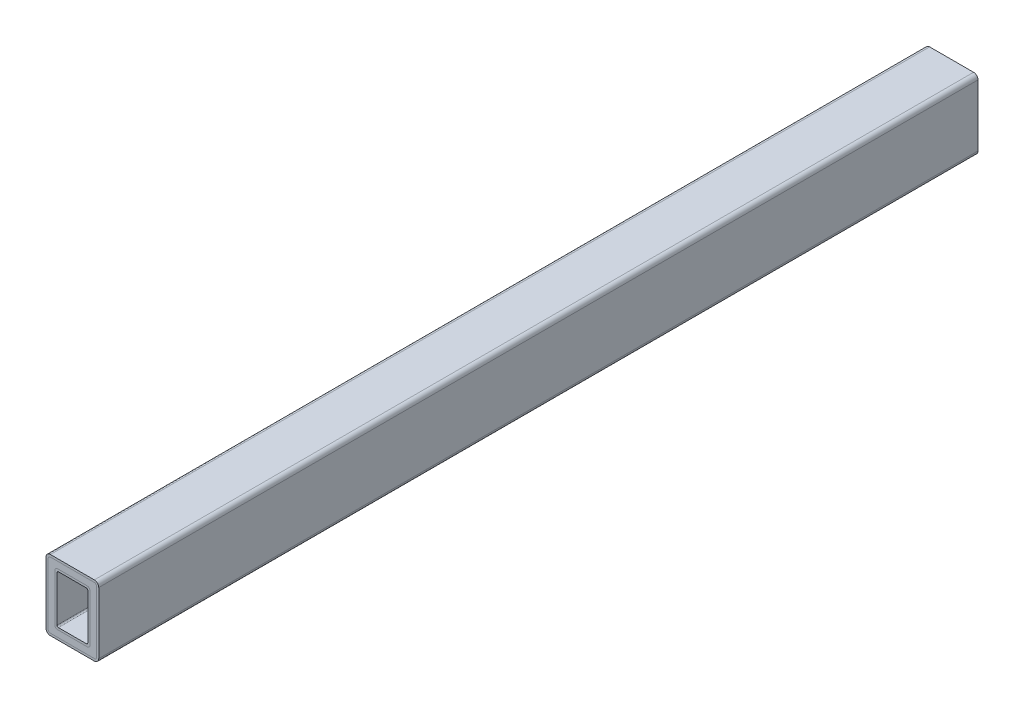
SolidWorks part; units mm, degrees
material "Plain Carbon Steel"
ref_plane "Front Plane" through (0, 0, 0) normal (0, 0, 1) x (1, 0, 0)
ref_plane "Top Plane" through (0, 0, 0) normal (0, 1, 0) x (1, 0, 0)
ref_plane "Right Plane" through (0, 0, 0) normal (1, 0, 0) x (0, 0, -1)
sketch "Sketch4" plane through (0, 0, 0) normal (0, 0, 1) x (1, 0, 0)
  line L4 (31.75, -47.6907) -> (-31.75, -47.6907)
  line L5 (34.925, 44.3843) -> (34.925, -44.5157)
  line L6 (-34.925, -44.5157) -> (-34.925, 44.3843)
  line L7 (-31.75, 47.5593) -> (31.75, 47.5593)
  line L8 (31.75, -50.8657) -> (-31.75, -50.8657)
  line L9 (38.1, 44.3843) -> (38.1, -44.5157)
  line L10 (-31.75, 50.7343) -> (31.75, 50.7343)
  line L11 (-38.1, -44.5157) -> (-38.1, 44.3843)
  arc A4 (-34.925, -44.5157) -> (-31.75, -47.6907) centre (-31.75, -44.5157) ccw
  arc A5 (31.75, -47.6907) -> (34.925, -44.5157) centre (31.75, -44.5157) ccw
  arc A6 (34.925, 44.3843) -> (31.75, 47.5593) centre (31.75, 44.3843) ccw
  arc A7 (-31.75, 47.5593) -> (-34.925, 44.3843) centre (-31.75, 44.3843) ccw
  arc A8 (-38.1, -44.5157) -> (-31.75, -50.8657) centre (-31.75, -44.5157) ccw
  arc A9 (31.75, -50.8657) -> (38.1, -44.5157) centre (31.75, -44.5157) ccw
  arc A10 (38.1, 44.3843) -> (31.75, 50.7343) centre (31.75, 44.3843) ccw
  arc A11 (-31.75, 50.7343) -> (-38.1, 44.3843) centre (-31.75, 44.3843) ccw
  dimension "D1" = 3.175
extrude "Boss-Extrude1" add sketch "Sketch4" along normal mid plane 1270 separate body
sketch "Sketch5" [suppressed] plane through (0, 50.7343, 0) normal (0, 1, 0) x (1, 0, 0)
  line L0 (0, 635) -> (0, 130) construction
  line L1 (31.75, 635) -> (-31.75, 635) construction
  line L2 (0, 130) -> (0, -130) construction
  line L3 (0, -130) -> (0, -635) construction
  line L4 (31.75, -635) -> (-31.75, -635) construction
  line L5 (-38.1, 130) -> (38.1, 130)
  line L6 (-38.1, -635) -> (-38.1, 635) construction
  line L7 (38.1, -635) -> (38.1, 635) construction
  line L8 (-38.1, -130) -> (38.1, -130)
  dimension "D1" = 260
split line "Split Line1" [suppressed]
sketch "Sketch6" [suppressed] plane through (0, 0, 0) normal (0, 0, 1) x (1, 0, 0)
  circle A0 centre (0, 0) radius 3.0965
extrude "Boss-Extrude2" [suppressed] add sketch "Sketch6" along normal mid plane 35.814 separate body
sketch "Sketch7" [suppressed] plane through (0, 0, 635) normal (0, 0, 1) x (1, 0, 0)
  line L0 (-31.75, -47.6907) -> (31.75, -47.6907) construction
  line L1 (34.925, -44.5157) -> (34.925, 44.3843) construction
  line L2 (-34.925, 44.3843) -> (-34.925, -44.5157) construction
  line L3 (31.75, 47.5593) -> (-31.75, 47.5593) construction
  line L4 (-31.75, -47.6907) -> (31.75, -47.6907)
  line L5 (34.925, -44.5157) -> (34.925, 44.3843)
  line L6 (-34.925, 44.3843) -> (-34.925, -44.5157)
  line L7 (31.75, 47.5593) -> (-31.75, 47.5593)
  arc A0 (-34.925, -44.5157) -> (-31.75, -47.6907) centre (-31.75, -44.5157) ccw construction
  arc A1 (31.75, -47.6907) -> (34.925, -44.5157) centre (31.75, -44.5157) ccw construction
  arc A2 (34.925, 44.3843) -> (31.75, 47.5593) centre (31.75, 44.3843) ccw construction
  arc A3 (-31.75, 47.5593) -> (-34.925, 44.3843) centre (-31.75, 44.3843) ccw construction
  arc A4 (-34.925, -44.5157) -> (-31.75, -47.6907) centre (-31.75, -44.5157) ccw
  arc A5 (31.75, -47.6907) -> (34.925, -44.5157) centre (31.75, -44.5157) ccw
  arc A6 (34.925, 44.3843) -> (31.75, 47.5593) centre (31.75, 44.3843) ccw
  arc A7 (-31.75, 47.5593) -> (-34.925, 44.3843) centre (-31.75, 44.3843) ccw
extrude "Boss-Extrude3" [suppressed] add sketch "Sketch7" against normal up to surface (1270 mm away) separate body
sketch "Sketch8" plane through (0, 0, 0) normal (0, 0, 1) x (1, 0, 0)
  line L0 (-31.75, 50.7343) -> (-31.75, 47.5593) construction
  line L1 (25.4, -38.1) -> (-25.4, -38.1)
  line L2 (25.4, -38.1) -> (25.4, 38.1)
  line L3 (25.4, 38.1) -> (-25.4, 38.1)
  line L4 (-25.4, -38.1) -> (-25.4, 38.1)
  line L5 (25.4, -38.1) -> (-25.4, 38.1) construction
  line L6 (25.4, 38.1) -> (-25.4, -38.1) construction
  line L7 (-22.225, 34.925) -> (-22.225, 38.1) construction
  line L8 (22.225, -34.925) -> (-22.225, -34.925)
  line L9 (22.225, -34.925) -> (22.225, 34.925)
  line L10 (22.225, 34.925) -> (-22.225, 34.925)
  line L11 (-22.225, -34.925) -> (-22.225, 34.925)
  line L12 (22.225, -34.925) -> (-22.225, 34.925) construction
  line L13 (22.225, 34.925) -> (-22.225, -34.925) construction
  line L14 (-22.225, 34.925) -> (-25.4, 34.925) construction
  point P0 (0, 0)
  point P10 (0, 0)
  dimension "D1" = 50.8
  dimension "D2" = 76.2
extrude "Boss-Extrude4" add sketch "Sketch8" against normal up to surface (1270 mm away) from surface at 635 separate body up to face at (0, -0.0657, -635) starting at face at (0, -0.0657, 635)
fillet "Fillet1" radius 4 4 edges at (-25.4, -38.1, 0) (25.4, -38.1, 0) (-25.4, 38.1, 0) (25.4, 38.1, 0)
fillet "Fillet2" radius 2 4 edges at (-22.225, -34.925, 0) (22.225, -34.925, 0) (22.225, 34.925, 0) (-22.225, 34.925, 0)
sketch "Sketch9" plane through (0, 0, -635) normal (0, 0, -1) x (-1, 0, 0)
  line L0 (31.75, -47.6907) -> (-31.75, -47.6907) construction
  line L1 (-34.925, -44.5157) -> (-34.925, 44.3843) construction
  line L2 (34.925, 44.3843) -> (34.925, -44.5157) construction
  line L3 (-31.75, 47.5593) -> (31.75, 47.5593) construction
  line L4 (31.75, -47.6907) -> (-31.75, -47.6907)
  line L5 (-34.925, -44.5157) -> (-34.925, 44.3843)
  line L6 (34.925, 44.3843) -> (34.925, -44.5157)
  line L7 (-31.75, 47.5593) -> (31.75, 47.5593)
  line L8 (21.4, -38.1) -> (-21.4, -38.1) construction
  line L9 (-25.4, -34.1) -> (-25.4, 34.1) construction
  line L10 (-21.4, 38.1) -> (21.4, 38.1) construction
  line L11 (25.4, 34.1) -> (25.4, -34.1) construction
  line L12 (21.4, -38.1) -> (-21.4, -38.1)
  line L13 (-25.4, -34.1) -> (-25.4, 34.1)
  line L14 (-21.4, 38.1) -> (21.4, 38.1)
  line L15 (25.4, 34.1) -> (25.4, -34.1)
  arc A0 (31.75, -47.6907) -> (34.925, -44.5157) centre (31.75, -44.5157) ccw construction
  arc A1 (-34.925, -44.5157) -> (-31.75, -47.6907) centre (-31.75, -44.5157) ccw construction
  arc A2 (-31.75, 47.5593) -> (-34.925, 44.3843) centre (-31.75, 44.3843) ccw construction
  arc A3 (34.925, 44.3843) -> (31.75, 47.5593) centre (31.75, 44.3843) ccw construction
  arc A4 (31.75, -47.6907) -> (34.925, -44.5157) centre (31.75, -44.5157) ccw
  arc A5 (-34.925, -44.5157) -> (-31.75, -47.6907) centre (-31.75, -44.5157) ccw
  arc A6 (-31.75, 47.5593) -> (-34.925, 44.3843) centre (-31.75, 44.3843) ccw
  arc A7 (34.925, 44.3843) -> (31.75, 47.5593) centre (31.75, 44.3843) ccw
  arc A8 (21.4, -38.1) -> (25.4, -34.1) centre (21.4, -34.1) ccw construction
  arc A9 (-25.4, -34.1) -> (-21.4, -38.1) centre (-21.4, -34.1) ccw construction
  arc A10 (-21.4, 38.1) -> (-25.4, 34.1) centre (-21.4, 34.1) ccw construction
  arc A11 (25.4, 34.1) -> (21.4, 38.1) centre (21.4, 34.1) ccw construction
  arc A12 (21.4, -38.1) -> (25.4, -34.1) centre (21.4, -34.1) ccw
  arc A13 (-25.4, -34.1) -> (-21.4, -38.1) centre (-21.4, -34.1) ccw
  arc A14 (-21.4, 38.1) -> (-25.4, 34.1) centre (-21.4, 34.1) ccw
  arc A15 (25.4, 34.1) -> (21.4, 38.1) centre (21.4, 34.1) ccw
extrude "Boss-Extrude5" add sketch "Sketch9" against normal up to surface (1270 mm away) separate body up to face at (0, -0.0657, 635)
equation "\"M5_tap\"=4.2mm\t\t\t\t\t\t\t' Below you can do mesurements as follows: cm, mm, ft, in, m, "
equation "\"M5_clearence\"=5.5mm"
equation "\"M6_tap\"=5mm"
equation "\"M6_clearence\"=6.6mm"
